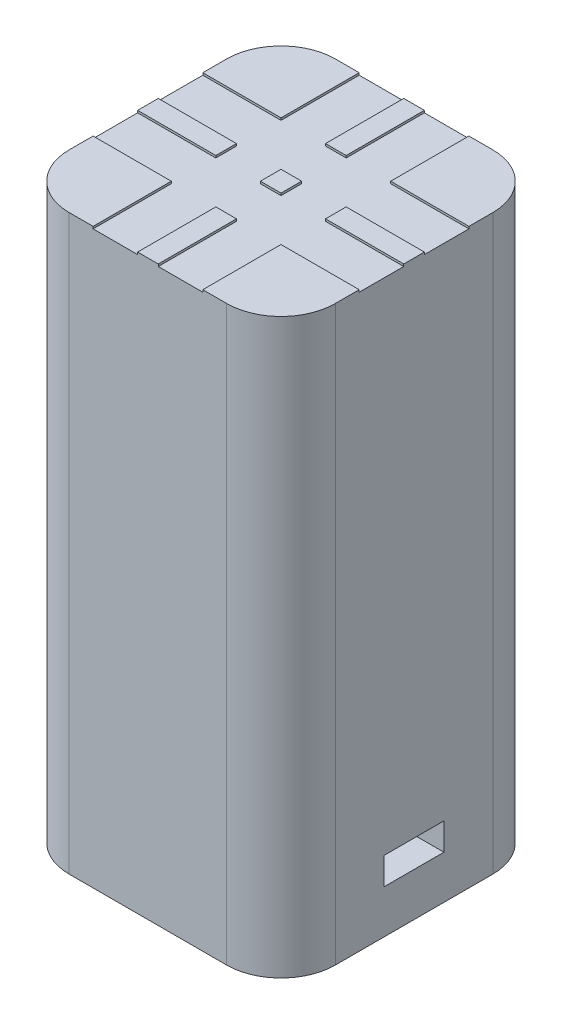
SolidWorks part; units mm, degrees
ref_plane "Front Plane" through (0, 0, 0) normal (0, 0, 1) x (1, 0, 0)
ref_plane "Top Plane" through (0, 0, 0) normal (0, 1, 0) x (1, 0, 0)
ref_plane "Right Plane" through (0, 0, 0) normal (1, 0, 0) x (0, 0, -1)
sketch "Sketch1" plane through (0, 0, 0) normal (0, 1, 0) x (1, 0, 0)
  line L1 (-12.25, -12.25) -> (12.25, -12.25)
  line L2 (-12.25, -12.25) -> (-12.25, 12.25)
  line L3 (-12.25, 12.25) -> (12.25, 12.25)
  line L4 (12.25, -12.25) -> (12.25, 12.25)
  line L5 (-12.25, -12.25) -> (12.25, 12.25) construction
  line L6 (-12.25, 12.25) -> (12.25, -12.25) construction
  point P0 (0, 0)
  dimension "D1" = 24.5
extrude "Boss-Extrude1" add sketch "Sketch1" along normal blind 52.75
sketch "Sketch3" plane through (0, 0, 0) normal (0, -1, 0) x (1, 0, 0)
  line L0 (0, 0) -> (7.5, 0) construction
  circle A0 centre (-7.5, 0) radius 1.3
  circle A1 centre (7.5, 0) radius 1.3
  dimension "D3" = 2.6
  dimension "D1" = 15
  dimension "D2" = 7.5
extrude "Cut-Extrude1" cut sketch "Sketch3" against normal blind 10
sketch "Sketch4" plane through (0, 52.75, 0) normal (0, 1, 0) x (1, 0, 0)
  line L0 (0, 12.25) -> (0, 0) construction
  line L1 (12.25, 12.25) -> (-12.25, 12.25) construction
  line L2 (0, 0) -> (12.25, 0) construction
  line L3 (12.25, -12.25) -> (12.25, 12.25) construction
  line L4 (0.95, 12.25) -> (0.95, 5.05)
  line L5 (12.25, 5.05) -> (12.25, 0.95)
  line L6 (5.05, 5.05) -> (5.05, 12.25)
  line L7 (0.95, 12.25) -> (5.05, 12.25)
  line L8 (0.95, 5.05) -> (-0.95, 5.05)
  line L9 (-0.95, 0.95) -> (0.95, 0.95)
  line L10 (0.95, 0.95) -> (0.95, -0.95)
  line L11 (5.05, -0.95) -> (5.05, 0.95)
  line L12 (5.05, 0.95) -> (12.25, 0.95)
  line L13 (5.05, 5.05) -> (12.25, 5.05)
  line L14 (5.05, -5.05) -> (12.25, -5.05)
  line L15 (5.05, -0.95) -> (12.25, -0.95)
  line L16 (-0.95, -0.95) -> (0.95, -0.95)
  line L17 (0.95, -5.05) -> (-0.95, -5.05)
  line L18 (0.95, -12.25) -> (5.05, -12.25)
  line L19 (5.05, -5.05) -> (5.05, -12.25)
  line L20 (12.25, -5.05) -> (12.25, -0.95)
  line L21 (0.95, -12.25) -> (0.95, -5.05)
  line L22 (-0.95, -12.25) -> (-0.95, -5.05)
  line L23 (-12.25, -5.05) -> (-12.25, -0.95)
  line L24 (-5.05, -5.05) -> (-5.05, -12.25)
  line L25 (-0.95, -12.25) -> (-5.05, -12.25)
  line L26 (-5.05, -0.95) -> (-12.25, -0.95)
  line L27 (-5.05, -5.05) -> (-12.25, -5.05)
  line L28 (-5.05, 5.05) -> (-12.25, 5.05)
  line L29 (-5.05, 0.95) -> (-12.25, 0.95)
  line L30 (-5.05, -0.95) -> (-5.05, 0.95)
  line L31 (-0.95, 0.95) -> (-0.95, -0.95)
  line L32 (-0.95, 12.25) -> (-5.05, 12.25)
  line L33 (-5.05, 5.05) -> (-5.05, 12.25)
  line L34 (-12.25, 5.05) -> (-12.25, 0.95)
  line L35 (-0.95, 12.25) -> (-0.95, 5.05)
  point P24 (5.05, 0)
  point P25 (0.95, 0)
  point P30 (-0.95, 0)
  point P31 (-5.05, 0)
  point P38 (0, -5.05)
  point P39 (0, -0.95)
  point P45 (0, 0.95)
  point P46 (0, 5.05)
  dimension "D1" = 4.1
  dimension "D2" = 1.9
  dimension "D3" = 1.9
extrude "Cut-Extrude2" cut sketch "Sketch4" against normal blind 0.2
fillet "Fillet1" radius 5 4 edges at (-12.25, 26.375, -12.25) (12.25, 26.375, -12.25) (12.25, 26.375, 12.25) (-12.25, 26.375, 12.25)
sketch "Sketch5" plane through (0, 0, 0) normal (0, -1, 0) x (1, 0, 0)
  line L0 (-4.3246, 0) -> (0, 0) construction
  line L1 (-10.6754, 0) -> (-9.0877, -2.75) construction
  line L2 (-9.0877, -2.75) -> (-5.9123, -2.75)
  line L3 (-5.9123, -2.75) -> (-4.3246, 0)
  line L4 (-4.3246, 0) -> (-5.9123, 2.75)
  line L5 (-5.9123, 2.75) -> (-9.0877, 2.75)
  line L6 (-9.0877, 2.75) -> (-10.6754, 0) construction
  line L7 (10.6754, 0) -> (9.0877, 2.75) construction
  line L8 (9.0877, 2.75) -> (5.9123, 2.75)
  line L9 (5.9123, 2.75) -> (4.3246, 0)
  line L10 (4.3246, 0) -> (5.9123, -2.75)
  line L11 (5.9123, -2.75) -> (9.0877, -2.75)
  line L12 (9.0877, -2.75) -> (10.6754, 0) construction
  line L13 (0, 0) -> (4.3246, 0) construction
  line L14 (-9.0877, 2.75) -> (-14.789, 2.75)
  line L15 (-14.789, 2.75) -> (-14.789, -2.75)
  line L16 (-14.789, -2.75) -> (-9.0877, -2.75)
  line L17 (9.0877, 2.75) -> (14.2813, 2.75)
  line L18 (14.2813, 2.75) -> (14.2813, -2.75)
  line L19 (14.2813, -2.75) -> (9.0877, -2.75)
  circle A0 centre (-7.5, 0) radius 2.75 construction
  circle A1 centre (7.5, 0) radius 2.75 construction
  dimension "D1" = 5.5
extrude "Cut-Extrude3" cut sketch "Sketch5" against normal blind 2.5 from offset 4 offset against normal yes
sketch "Sketch6" plane through (-12.25, 0, 0) normal (-1, 0, 0) x (0, 0, 1)
  line L0 (0, 45) -> (0, 0) construction
  circle A0 centre (0, 45) radius 2.5
  dimension "D1" = 5
  dimension "D2" = 45
extrude "Cut-Extrude4" cut sketch "Sketch6" against normal blind 7
